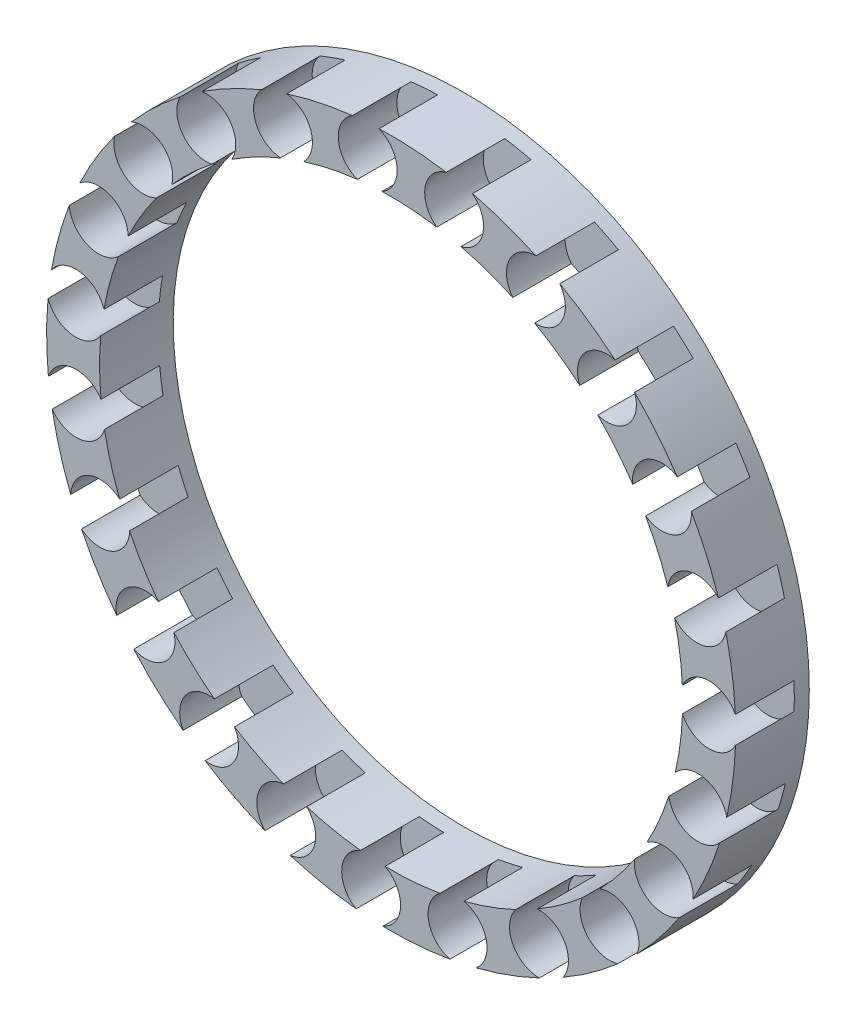
SolidWorks part; units mm, degrees
ref_plane "前视基准面" through (0, 0, 0) normal (0, 0, 1) x (1, 0, 0)
ref_plane "上视基准面" through (0, 0, 0) normal (0, 1, 0) x (1, 0, 0)
ref_plane "右视基准面" through (0, 0, 0) normal (1, 0, 0) x (0, 0, -1)
sketch "草图1" plane through (0, 0, 0) normal (0, 0, 1) x (1, 0, 0)
  circle A0 centre (0, 0) radius 23.4
  circle A1 centre (0, 0) radius 19.8
extrude "凸台-拉伸1" add sketch "草图1" along normal blind 5
ref_plane "基准面1" through (21.6, 0, 0) normal (1, 0, 0) x (0, 0, -1)
sketch "草图2" plane through (21.6, 0, 0) normal (1, 0, 0) x (0, 0, -1)
  line L1 (-5.0203, 0.1176) -> (-1.0203, 0.1176)
  line L2 (-5.0203, 0.1176) -> (-5.0203, 2.1176)
  line L3 (-5.0203, 2.1176) -> (-1.0203, 2.1176)
  line L4 (-1.0203, 0.1176) -> (-1.0203, 2.1176)
  dimension "D1" = 4
  dimension "D2" = 2
revolve "切除-旋转1" cut sketch "草图2" angle 360 about L1
pattern_circular "阵列(圆周)1" count 23 over 360 about axis through (0, 0, 0) along (0, 0, 1) of "切除-旋转1"
